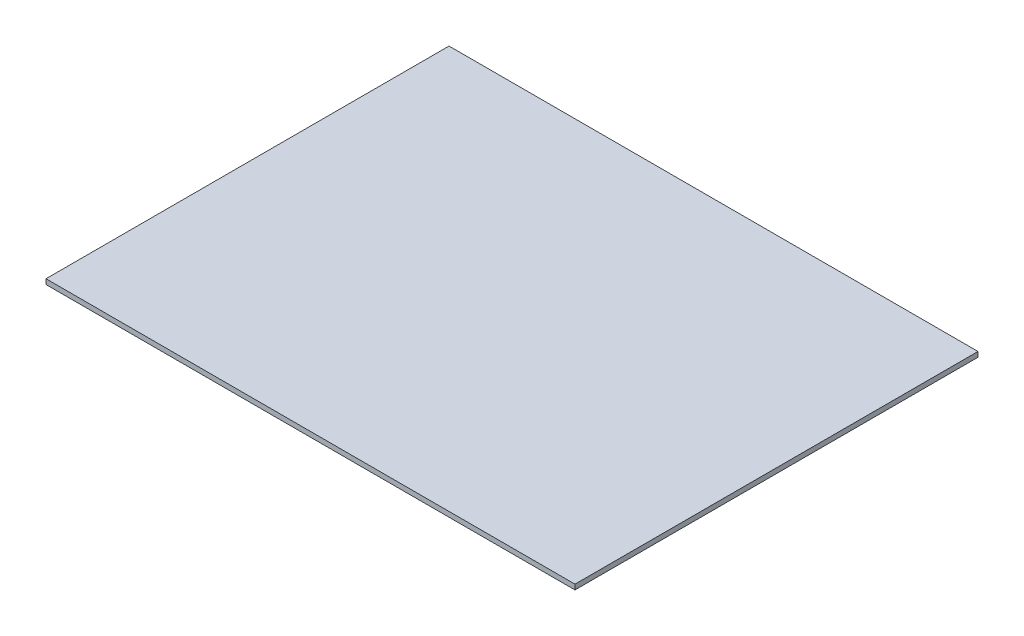
SolidWorks part; units mm, degrees
ref_plane "Alzado" through (0, 0, 0) normal (0, 0, 1) x (1, 0, 0)
ref_plane "Planta" through (0, 0, 0) normal (0, 1, 0) x (1, 0, 0)
ref_plane "Vista lateral" through (0, 0, 0) normal (1, 0, 0) x (0, 0, -1)
sketch "Croquis1" plane through (0, 0, 0) normal (0, 1, 0) x (1, 0, 0)
  line L1 (0, 0) -> (210, 0)
  line L2 (0, 0) -> (0, 160)
  line L3 (0, 160) -> (210, 160)
  line L4 (210, 0) -> (210, 160)
  dimension "D1" = 160
  dimension "D2" = 210
extrude "Saliente-Extruir1" add sketch "Croquis1" along normal blind 2
